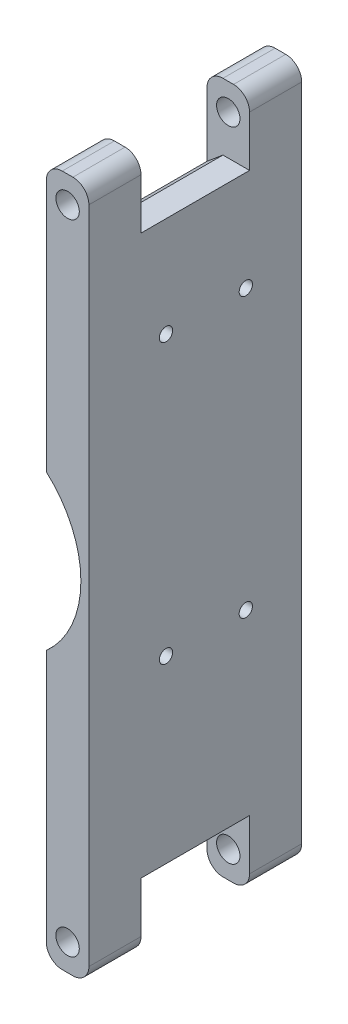
SolidWorks part; units mm, degrees
ref_plane "Front Plane" through (0, 0, 0) normal (0, 0, 1) x (1, 0, 0)
ref_plane "Top Plane" through (0, 0, 0) normal (0, 1, 0) x (1, 0, 0)
ref_plane "Right Plane" through (0, 0, 0) normal (1, 0, 0) x (0, 0, -1)
sketch "Sketch1" plane through (0, 0, 0) normal (0, 0, 1) x (1, 0, 0)
  line L1 (-4, 65) -> (4, 65)
  line L2 (-4, 65) -> (-4, -65)
  line L3 (-4, -65) -> (4, -65)
  line L4 (4, 65) -> (4, -65)
  line L5 (-4, 65) -> (4, -65) construction
  line L6 (-4, -65) -> (4, 65) construction
  point P0 (0, 0)
  dimension "D1" = 8
  dimension "D2" = 130
extrude "Boss-Extrude1" add sketch "Sketch1" against normal blind 40
sketch "Sketch2" plane through (4, 0, 0) normal (1, 0, 0) x (0, 0, -1)
  line L0 (40, 65) -> (0, 65) construction
  line L1 (9.8, 77.5) -> (30.2, 77.5)
  line L2 (9.8, 77.5) -> (9.8, 52.5)
  line L3 (9.8, 52.5) -> (30.2, 52.5)
  line L4 (30.2, 77.5) -> (30.2, 52.5)
  line L5 (9.8, 77.5) -> (30.2, 52.5) construction
  line L6 (9.8, 52.5) -> (30.2, 77.5) construction
  line L7 (0, 0) -> (54.2084, 0) construction
  line L8 (9.8, -52.5) -> (30.2, -77.5) construction
  line L9 (9.8, -77.5) -> (30.2, -52.5) construction
  line L10 (30.2, -77.5) -> (30.2, -52.5)
  line L11 (9.8, -52.5) -> (30.2, -52.5)
  line L12 (9.8, -77.5) -> (9.8, -52.5)
  line L13 (9.8, -77.5) -> (30.2, -77.5)
  line L14 (40, -65) -> (40, 65) construction
  point P0 (20, 65)
  point P14 (20, -65)
  dimension "D1" = 25
  dimension "D2" = 9.8
extrude "Cut-Extrude1" cut sketch "Sketch2" against normal through all
fillet "Fillet1" radius 3 8 edges at (-4, -65, -35.1) (4, -65, -35.1) (-4, -65, -4.9) (4, -65, -4.9) (-4, 65, -4.9) (-4, 65, -35.1) (4, 65, -35.1) (4, 65, -4.9)
sketch "Sketch3" plane through (0, 0, 0) normal (0, 0, 1) x (1, 0, 0)
  line L0 (0, 0) -> (0, 60) construction
  line L1 (1, 65) -> (-1, 65) construction
  line L2 (0, 0) -> (14.6507, 0) construction
  circle A0 centre (0, 60) radius 2.2
  circle A1 centre (0, -60) radius 2.2
  dimension "D1" = 4.4
  dimension "D2" = 5
extrude "Cut-Extrude2" cut sketch "Sketch3" against normal through all
sketch "Sketch4" plane through (0, 0, 0) normal (0, 0, 1) x (1, 0, 0)
  line L0 (0, 0) -> (-17, 0) construction
  circle A0 centre (-17, 0) radius 19.5
  dimension "D2" = 39
  dimension "D1" = 17
extrude "Cut-Extrude3" cut sketch "Sketch4" against normal blind 7.3
sketch "Sketch6" plane through (-4, 0, 0) normal (-1, 0, 0) x (0, 0, 1)
  line L0 (-52.5403, 7.5) -> (8.8185, 7.5) construction
  line L1 (-22, 7.5) -> (-22, 43.2) construction
  line L2 (-40, 62) -> (-40, -62) construction
  line L3 (-40, 65) -> (-30.2, 65) construction
  circle A1 centre (-29.5, 33.7) radius 1.25
  circle A3 centre (-29.5, -18.7) radius 1.25
  circle A4 centre (-14.5, 33.7) radius 1.25
  circle A5 centre (-14.5, -18.7) radius 1.25
  dimension "D1" = 2.5
  dimension "D3" = 15
  dimension "D5" = 31.3
  dimension "D2" = 26.2
  dimension "D4" = 18
extrude "Cut-Extrude5" cut sketch "Sketch6" against normal up to next
chamfer "Chamfer1" distance 3 angle 40 2 edges at (-4, 52.5, -20) (-4, -52.5, -20)
